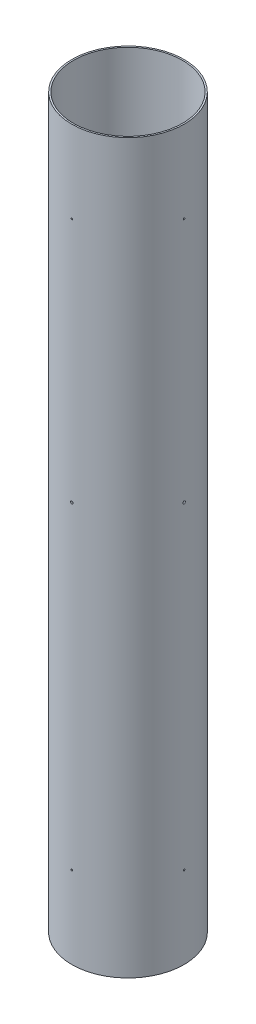
SolidWorks part; units mm, degrees
material "A-Glass Fiber"
ref_plane "Front Plane" through (0, 0, 0) normal (0, 0, 1) x (1, 0, 0)
ref_plane "Top Plane" through (0, 0, 0) normal (0, 1, 0) x (1, 0, 0)
ref_plane "Right Plane" through (0, 0, 0) normal (1, 0, 0) x (0, 0, -1)
sketch "Sketch1" plane through (0, 0, 0) normal (0, 1, 0) x (1, 0, 0)
  circle A0 centre (0, 0) radius 76.1746
  circle A1 centre (0, 0) radius 78.359
  dimension "D1" = 156.718
  dimension "D2" = 152.3492
extrude "Boss-Extrude1" add sketch "Sketch1" along normal blind 1016
ref_axis "Axis1" through (0, 1016, 0) along (0, -1, 0)
sketch "Sketch3" plane through (0, 0, 0) normal (0, 0, 1) x (1, 0, 0)
  line L0 (0, 558.8) -> (0, 1016) construction
  line L1 (78.359, 1016) -> (-78.359, 1016) construction
  line L2 (0, 0) -> (0, 114.3) construction
  circle A0 centre (0, 558.8) radius 1.75
  circle A1 centre (0, 114.3) radius 1.0922
  circle A2 centre (0, 901.7) radius 1.0922
  dimension "D2" = 3.5
  dimension "D3" = 2.1844
  dimension "D4" = 2.1844
  dimension "D1" = 457.2
  dimension "D5" = 114.3
extrude "Cut-Extrude1" cut sketch "Sketch3" against normal through all
pattern_circular "CirPattern1" count 4 over 360 about axis through (0, 1016, 0) along (0, -1, 0) of "Cut-Extrude1"
equation "\"Fwd_Tube_Length\" = 40in"
equation "\"D1@Boss-Extrude1\" = \"Fwd_Tube_Length\""
equation "\"BKHD_Screw_Diam\"= 3.5mm"
equation "\"Fwd_BKHD_From_Top\" = 18in"
equation "\"D2@Sketch3\"=\"BKHD_Screw_Diam\""
equation "\"D1@Sketch3\"=\"Fwd_BKHD_From_Top\""
equation "\"Bodytube_OD\" = 6.17in"
equation "\"Bodytube_ID\" = 5.998in"
equation "\"D2@Sketch1\"=\"Bodytube_ID\""
equation "\"D1@Sketch1\"=\"Bodytube_OD\""
equation "\"Shear_Screw_Diameter\" = 0.086in"
equation "\"D3@Sketch3\"=\"Shear_Screw_Diameter\""
equation "\"D4@Sketch3\"=\"Shear_Screw_Diameter\""
equation "\"Shear_Screw_Coupler_Location\" = 4.5in"
equation "\"D5@Sketch3\"=\"Shear_Screw_Coupler_Location\""
